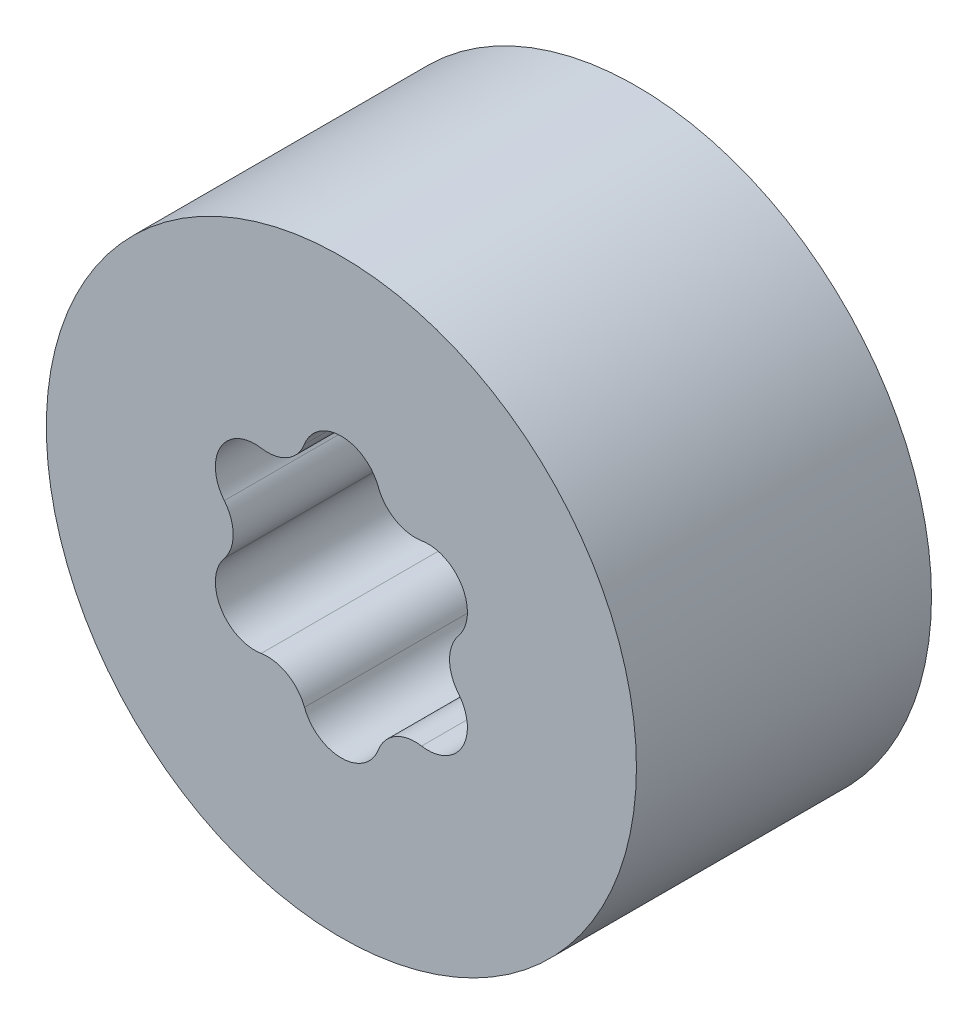
SolidWorks part; units mm, degrees
material "NEOPRENE"
ref_plane "Front Plane" through (0, 0, 0) normal (0, 0, 1) x (1, 0, 0)
ref_plane "Top Plane" through (0, 0, 0) normal (0, 1, 0) x (1, 0, 0)
ref_plane "Right Plane" through (0, 0, 0) normal (1, 0, 0) x (0, 0, -1)
sketch "Sketch1" plane through (0, 0, 0) normal (0, 0, 1) x (1, 0, 0)
  circle A0 centre (0, 0) radius 5
  circle A1 centre (0, 0) radius 19.05
  dimension "D1" = 10
  dimension "D2" = 38.1
extrude "Boss-Extrude1" add sketch "Sketch1" along normal mid plane 19.05
sketch "Sketch2" plane through (0, 0, -9.525) normal (0, 0, -1) x (-1, 0, 0)
  arc A12 (-2.3829, -7.3535) -> (-5.1769, -5.7405) centre (-4.7659, -8.2547) ccw
  arc A13 (-7.5598, -1.6131) -> (-5.1769, -5.7405) centre (-5.5879, -3.2262) ccw
  arc A14 (-7.5598, -1.6131) -> (-7.5598, 1.6131) centre (-9.5317, 0) ccw
  arc A15 (-5.1769, 5.7405) -> (-7.5598, 1.6131) centre (-5.5879, 3.2262) ccw
  arc A16 (-5.1769, 5.7405) -> (-2.3829, 7.3535) centre (-4.7659, 8.2547) ccw
  arc A17 (2.3829, 7.3535) -> (-2.3829, 7.3535) centre (0, 6.4524) ccw
  arc A18 (2.3829, 7.3535) -> (5.1769, 5.7405) centre (4.7659, 8.2547) ccw
  arc A19 (7.5598, 1.6131) -> (5.1769, 5.7405) centre (5.5879, 3.2262) ccw
  arc A20 (7.5598, 1.6131) -> (7.5598, -1.6131) centre (9.5317, 0) ccw
  arc A21 (5.1769, -5.7405) -> (7.5598, -1.6131) centre (5.5879, -3.2262) ccw
  arc A22 (5.1769, -5.7405) -> (2.3829, -7.3535) centre (4.7659, -8.2547) ccw
  arc A23 (-2.3829, -7.3535) -> (2.3829, -7.3535) centre (0, -6.4524) ccw
  arc A24 (-2.3829, -7.3535) -> (-5.1769, -5.7405) centre (-4.7659, -8.2547) ccw
  arc A25 (-7.5598, -1.6131) -> (-5.1769, -5.7405) centre (-5.5879, -3.2262) ccw
  arc A26 (-7.5598, -1.6131) -> (-7.5598, 1.6131) centre (-9.5317, 0) ccw
  arc A27 (-5.1769, 5.7405) -> (-7.5598, 1.6131) centre (-5.5879, 3.2262) ccw
  arc A28 (-5.1769, 5.7405) -> (-2.3829, 7.3535) centre (-4.7659, 8.2547) ccw
  arc A29 (2.3829, 7.3535) -> (-2.3829, 7.3535) centre (0, 6.4524) ccw
  arc A30 (2.3829, 7.3535) -> (5.1769, 5.7405) centre (4.7659, 8.2547) ccw
  arc A31 (7.5598, 1.6131) -> (5.1769, 5.7405) centre (5.5879, 3.2262) ccw
  arc A32 (7.5598, 1.6131) -> (7.5598, -1.6131) centre (9.5317, 0) ccw
  arc A33 (5.1769, -5.7405) -> (7.5598, -1.6131) centre (5.5879, -3.2262) ccw
  arc A34 (5.1769, -5.7405) -> (2.3829, -7.3535) centre (4.7659, -8.2547) ccw
  arc A35 (-2.3829, -7.3535) -> (2.3829, -7.3535) centre (0, -6.4524) ccw
  dimension "D1" = 0
extrude "Cut-Extrude1" cut sketch "Sketch2" against normal through all
